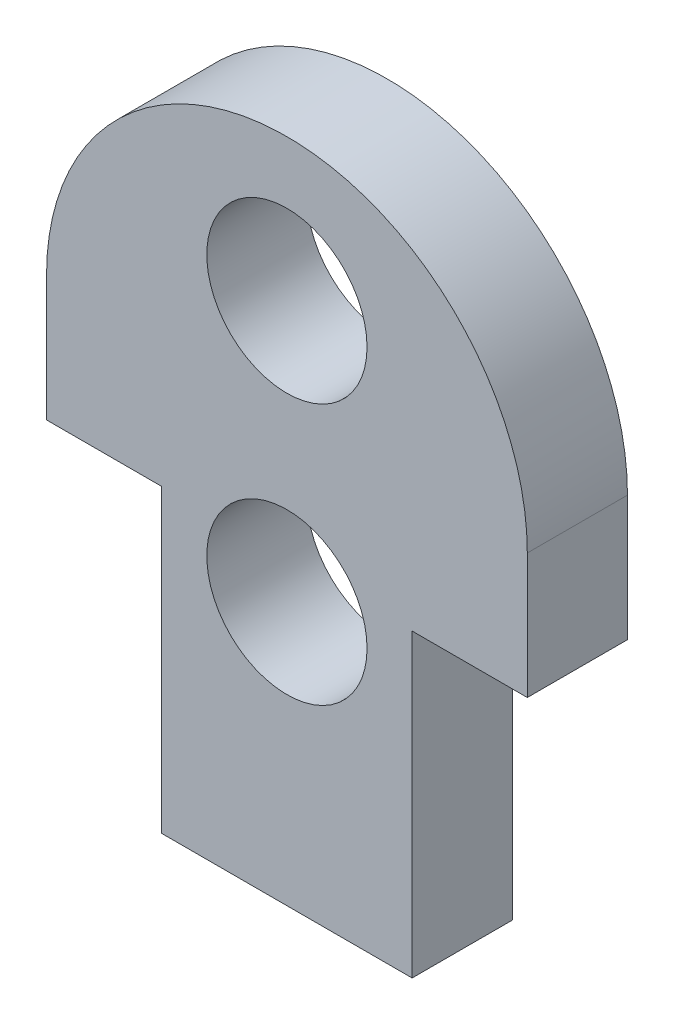
SolidWorks part; units mm, degrees
ref_plane "Front Plane" through (0, 0, 0) normal (0, 0, 1) x (1, 0, 0)
ref_plane "Top Plane" through (0, 0, 0) normal (0, 1, 0) x (1, 0, 0)
ref_plane "Right Plane" through (0, 0, 0) normal (1, 0, 0) x (0, 0, -1)
sketch "Sketch1" plane through (0, 0, 0) normal (0, 0, 1) x (1, 0, 0)
  line L0 (0, 0) -> (10, 0)
  line L1 (0, 0) -> (0, 4)
  line L2 (0, 4) -> (-2.5, 4)
  line L3 (3.3546, 18.0712) -> (6.6454, 18.0712) construction
  line L4 (-2.5, 4) -> (-2.5, 8)
  line L5 (-2.5, 8) -> (0, 8)
  line L6 (0, 8) -> (0, 12)
  line L7 (5, 0) -> (5, 27) construction
  line L8 (10, 0) -> (10, 4)
  line L9 (10, 4) -> (12.5, 4)
  line L10 (12.5, 4) -> (12.5, 8)
  line L11 (12.5, 8) -> (10, 8)
  line L12 (3.3546, 23.7712) -> (1.7091, 20.9212) construction
  line L13 (8.2909, 10.5) -> (6.6454, 13.35) construction
  line L14 (6.6454, 13.35) -> (3.3546, 13.35) construction
  line L15 (3.3546, 13.35) -> (1.7091, 10.5) construction
  line L16 (1.7091, 10.5) -> (3.3546, 7.65) construction
  line L17 (3.3546, 7.65) -> (6.6454, 7.65) construction
  line L18 (6.6454, 7.65) -> (8.2909, 10.5) construction
  line L19 (1.7091, 20.9212) -> (3.3546, 18.0712) construction
  line L20 (0, 12) -> (-4.6, 12)
  line L21 (10, 8) -> (10, 12)
  line L22 (6.6454, 18.0712) -> (8.2909, 20.9212) construction
  line L23 (8.2909, 20.9212) -> (6.6454, 23.7712) construction
  line L24 (6.6454, 23.7712) -> (3.3546, 23.7712) construction
  line L25 (10, 12) -> (14.6, 12)
  line L26 (-4.6, 12) -> (-4.6, 17)
  line L27 (14.6, 12) -> (14.6, 17)
  line L28 (3.3546, 23.7712) -> (6.6454, 18.0712) construction
  line L29 (6.6454, 23.7712) -> (3.3546, 18.0712) construction
  line L30 (3.3546, 13.35) -> (6.6454, 7.65) construction
  line L31 (6.6454, 13.35) -> (3.3546, 7.65) construction
  circle A0 centre (5, 20.9212) radius 3 construction
  arc A1 (14.6, 17) -> (-4.6, 17) centre (5, 17) ccw
  circle A2 centre (5, 10.5) radius 3 construction
  dimension "D5" = 2.5
  dimension "D3" = 6
  dimension "D2" = 5.7
  dimension "D8" = 4.6
  dimension "D9" = 4
  dimension "D10" = 4
  dimension "D12" = 2.5
extrude "Boss-Extrude1" add sketch "Sketch1" along normal blind 4
sketch "Sketch2" plane through (0, 0, 4) normal (0, 0, 1) x (1, 0, 0)
  line L0 (-2.5, 8) -> (0, 8)
  line L1 (0, 8) -> (0, 4)
  line L2 (0, 4) -> (-2.5, 4)
  line L3 (-2.5, 4) -> (-2.5, 8)
  line L4 (10, 8) -> (12.5, 8)
  line L5 (12.5, 8) -> (12.5, 4)
  line L6 (12.5, 4) -> (10, 4)
  line L7 (10, 4) -> (10, 8)
extrude "Cut-Extrude1" cut sketch "Sketch2" against normal up to surface (4 mm away) up to face at (5, 8.725, 0)
sketch "Sketch3" plane through (0, 0, 0) normal (0, 0, 1) x (1, 0, 0)
  circle A0 centre (5, 20.9212) radius 3.2
  circle A2 centre (5, 10.5) radius 3.2
  dimension "D1" = 6.4
  dimension "D2" = 10.5
  dimension "D3" = 5
  dimension "D4" = 10.4212
extrude "Cut-Extrude2" cut sketch "Sketch3" along normal through all
equation "\"D8@Sketch1\"= 5 - \"tol2@parametersSketch@prostheticParameters.SLDPRT\""
equation "\"D1@Sketch3\"= 6 + \"tol1@parametersSketch@prostheticParameters.SLDPRT\""
